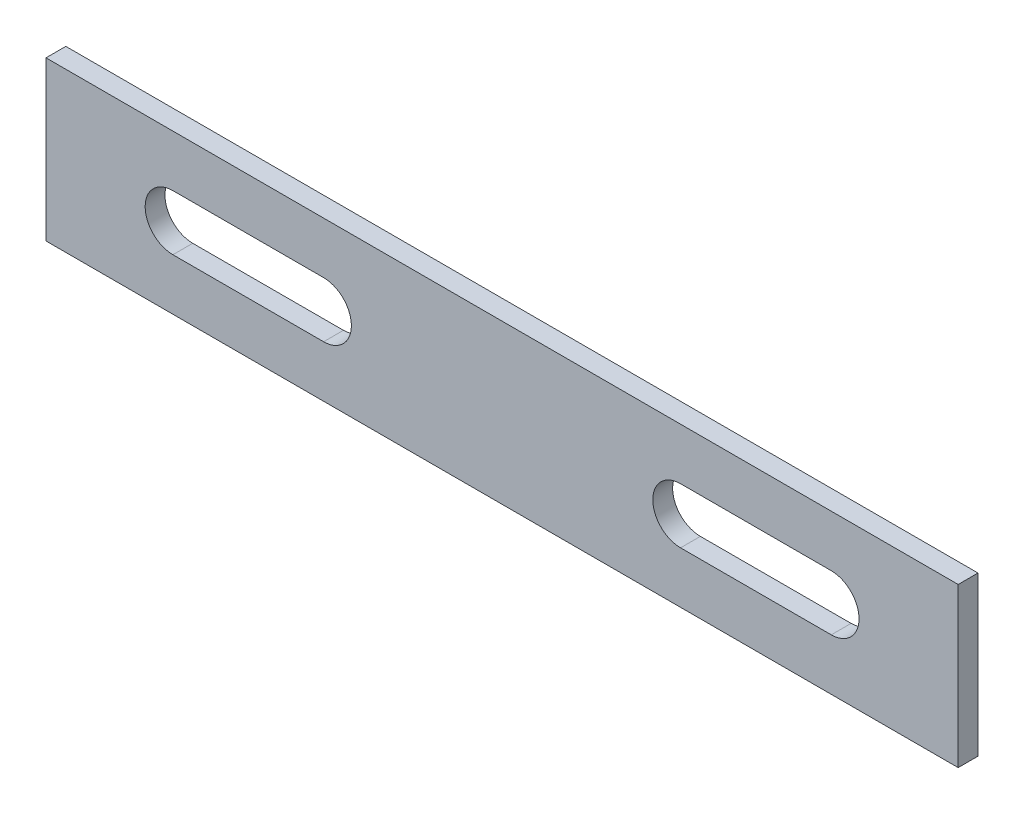
SolidWorks part; units mm, degrees
ref_plane "Plan de face" through (0, 0, 0) normal (0, 0, 1) x (1, 0, 0)
ref_plane "Plan de dessus" through (0, 0, 0) normal (0, 1, 0) x (1, 0, 0)
ref_plane "Plan de droite" through (0, 0, 0) normal (1, 0, 0) x (0, 0, -1)
sketch "Esquisse1" plane through (0, 0, 0) normal (0, 0, 1) x (1, 0, 0)
  line L0 (-115, 0) -> (115, 0)
other "Elément mécano-soudé1"
ref_plane "Plan1" through (-115, 0, 0) normal (1, 0, 0) x (0, 1, 0)
sketch "plat" plane through (-115, 0, 0) normal (1, 0, 0) x (0, 1, 0)
  line L0 (-20, 0) -> (20, 0) construction
  line L1 (-20, 2.5) -> (20, 2.5)
  line L2 (-20, 2.5) -> (-20, -2.5)
  line L3 (-20, -2.5) -> (20, -2.5)
  line L4 (20, 2.5) -> (20, -2.5)
  line L5 (0, 2.5) -> (0, -2.5) construction
  point P8 (0, 0)
  dimension "B" = 40
  dimension "A" = 5
sketch "Esquisse2" plane through (0, 0, 0) normal (0, 0, 1) x (1, 0, 0)
  line L0 (-83, 0) -> (-45, 0) construction
  line L1 (-115, 0) -> (115, 0) construction
  line L2 (-83, 7) -> (-45, 7)
  line L3 (-83, -7) -> (-45, -7)
  line L4 (-115, -20) -> (-115, 20) construction
  line L5 (0, 20) -> (0, -19.7459) construction
  line L6 (115, 20) -> (-115, 20) construction
  line L7 (0, -2.75) -> (0, 2.75) construction
  line L8 (83, 0) -> (45, 0) construction
  line L9 (83, 7) -> (45, 7)
  line L10 (83, -7) -> (45, -7)
  arc A0 (-83, 7) -> (-83, -7) centre (-83, 0) ccw
  arc A1 (-45, -7) -> (-45, 7) centre (-45, 0) ccw
  arc A2 (83, 7) -> (83, -7) centre (83, 0) cw
  arc A3 (45, -7) -> (45, 7) centre (45, 0) cw
  point P4 (-64, 0)
  point P20 (64, 0)
  dimension "D3" = 7
  dimension "D1" = 32
  dimension "D2" = 38
extrude "Enlèv. mat.-Extru.1" cut sketch "Esquisse2" against normal through all both and the other way through all
